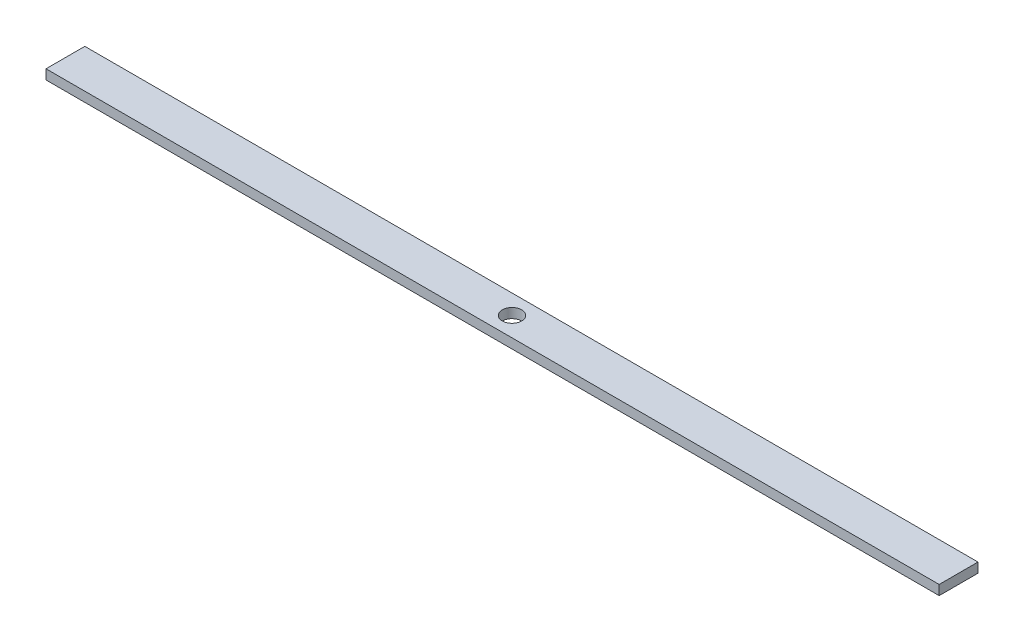
SolidWorks part; units mm, degrees
material "6061-T6 (SS)"
ref_plane "Front Plane" through (0, 0, 0) normal (0, 0, 1) x (1, 0, 0)
ref_plane "Top Plane" through (0, 0, 0) normal (0, 1, 0) x (1, 0, 0)
ref_plane "Right Plane" through (0, 0, 0) normal (1, 0, 0) x (0, 0, -1)
sketch "Sketch1" plane through (0, 0, 0) normal (0, 1, 0) x (1, 0, 0)
  line L1 (-292.1, 12.7) -> (292.1, 12.7)
  line L2 (-292.1, 12.7) -> (-292.1, -12.7)
  line L3 (-292.1, -12.7) -> (292.1, -12.7)
  line L4 (292.1, 12.7) -> (292.1, -12.7)
  line L5 (-292.1, 12.7) -> (292.1, -12.7) construction
  line L6 (-292.1, -12.7) -> (292.1, 12.7) construction
  circle A0 centre (0, 0) radius 6.35
  point P0 (0, 0)
  dimension "D1" = 25.4
  dimension "D2" = 584.2
extrude "Boss-Extrude1" add sketch "Sketch1" along normal blind 6.35
